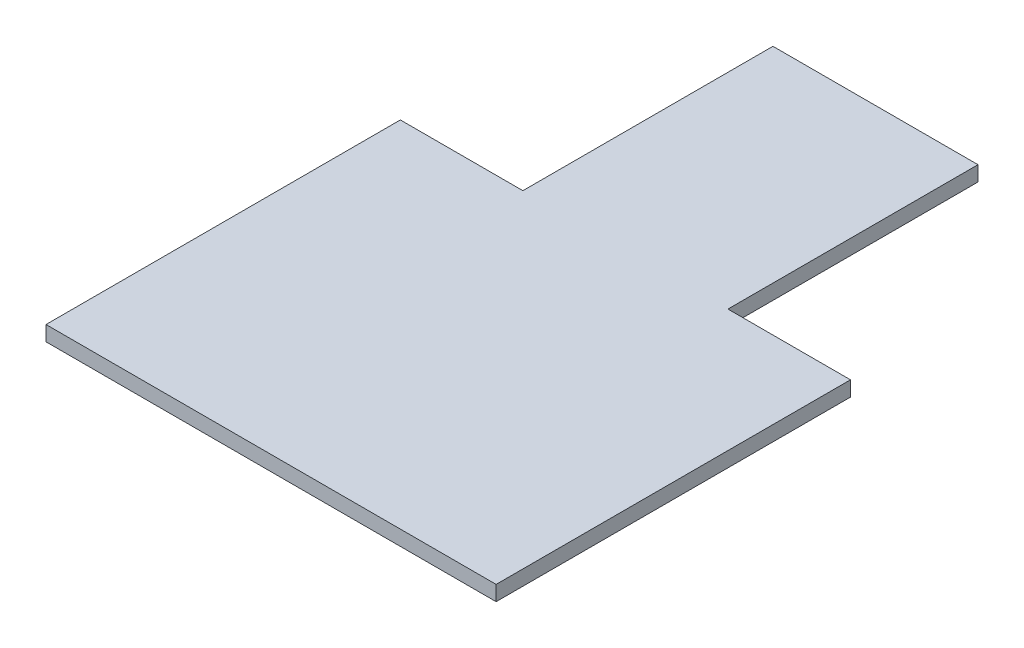
SolidWorks part; units mm, degrees
ref_plane "Front Plane" through (0, 0, 0) normal (0, 0, 1) x (1, 0, 0)
ref_plane "Top Plane" through (0, 0, 0) normal (0, 1, 0) x (1, 0, 0)
ref_plane "Right Plane" through (0, 0, 0) normal (1, 0, 0) x (0, 0, -1)
sketch "Sketch1" plane through (0, 0, 0) normal (0, 1, 0) x (1, 0, 0)
  line L0 (0, 60.8046) -> (0, -60.046) construction
  line L1 (20.5, 60.8046) -> (-20.5, 60.8046)
  line L2 (-20.5, 60.8046) -> (-20.5, 10.8046)
  line L3 (-20.5, 10.8046) -> (-45, 10.8046)
  line L4 (-45, 10.8046) -> (-45, -60.046)
  line L5 (-45, -60.046) -> (45, -60.046)
  line L6 (45, 10.8046) -> (45, -60.046)
  line L7 (20.5, 10.8046) -> (45, 10.8046)
  line L8 (20.5, 60.8046) -> (20.5, 10.8046)
  dimension "D1" = 41
  dimension "D2" = 50
  dimension "D3" = 90
extrude "Boss-Extrude1" add sketch "Sketch1" along normal blind 3
